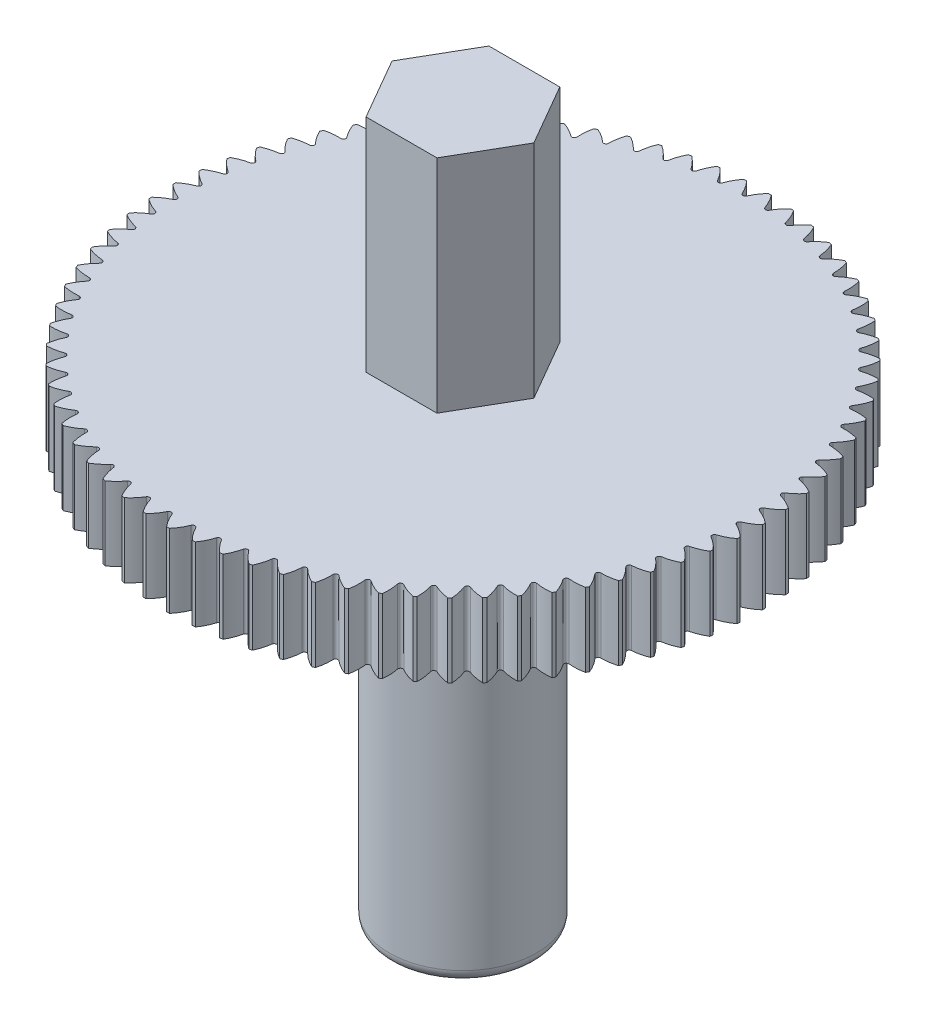
SolidWorks part; units mm, degrees
ref_plane "Front Plane" through (0, 0, 0) normal (0, 0, 1) x (1, 0, 0)
ref_plane "Top Plane" through (0, 0, 0) normal (0, 1, 0) x (1, 0, 0)
ref_plane "Right Plane" through (0, 0, 0) normal (1, 0, 0) x (0, 0, -1)
sketch "Sketch1" plane through (0, 0, 0) normal (0, 0, 1) x (1, 0, 0)
  line L0 (0, 0) -> (0, 29)
  line L1 (0, 29) -> (3, 29)
  line L2 (3, 29) -> (3, 20)
  line L3 (3, 20) -> (12, 20)
  line L4 (12, 20) -> (12, 17)
  line L5 (12, 17) -> (3, 17)
  line L6 (3, 17) -> (3, 0)
  line L7 (3, 0) -> (0, 0)
  dimension "D1" = 3
  dimension "D2" = 29
  dimension "D3" = 3
  dimension "D4" = 9
  dimension "D5" = 17
revolve "Revolve1" add sketch "Sketch1" angle 360 about L0
sketch "Sketch2" plane through (0, 20, 0) normal (0, 1, 0) x (1, 0, 0)
  line L0 (0, 0) -> (0, 12) construction
  line L1 (-0.45, 12) -> (0.45, 12)
  circle A0 centre (0, 0) radius 12 construction
  arc A1 (0.45, 12) -> (0.0912, 11.459) centre (1.9153, 10.6388) ccw
  arc A2 (0.0912, 11.459) -> (-0.0912, 11.459) centre (0, 11.5) cw
  arc A3 (-0.45, 12) -> (-0.0912, 11.459) centre (-1.9153, 10.6388) cw
  dimension "D2" = 0.1
  dimension "D3" = 2
  dimension "D1" = 0.9
  dimension "D4" = 0.5
extrude "Cut-Extrude1" cut sketch "Sketch2" against normal blind 10
pattern_circular "CirPattern1" count 75 over 360 about axis through (0, 0, 0) along (0, 1, 0) of "Cut-Extrude1"
sketch "Sketch3" plane through (0, 29, 0) normal (0, 1, 0) x (1, 0, 0)
  line L1 (-1.4434, 2.5) -> (-2.8868, 0)
  line L2 (-2.8868, 0) -> (-1.4434, -2.5)
  line L3 (-1.4434, -2.5) -> (1.4434, -2.5)
  line L4 (1.4434, -2.5) -> (2.8868, 0)
  line L5 (2.8868, 0) -> (1.4434, 2.5)
  line L6 (1.4434, 2.5) -> (-1.4434, 2.5)
  circle A0 centre (0, 0) radius 2.5 construction
  circle A1 centre (0, 0) radius 3 construction
  circle A2 centre (0, 0) radius 3
  dimension "D1" = 5
extrude "Cut-Extrude2" cut sketch "Sketch3" against normal blind 9
fillet "Fillet1" radius 0.5 1 edges at (0, 0, -3)
